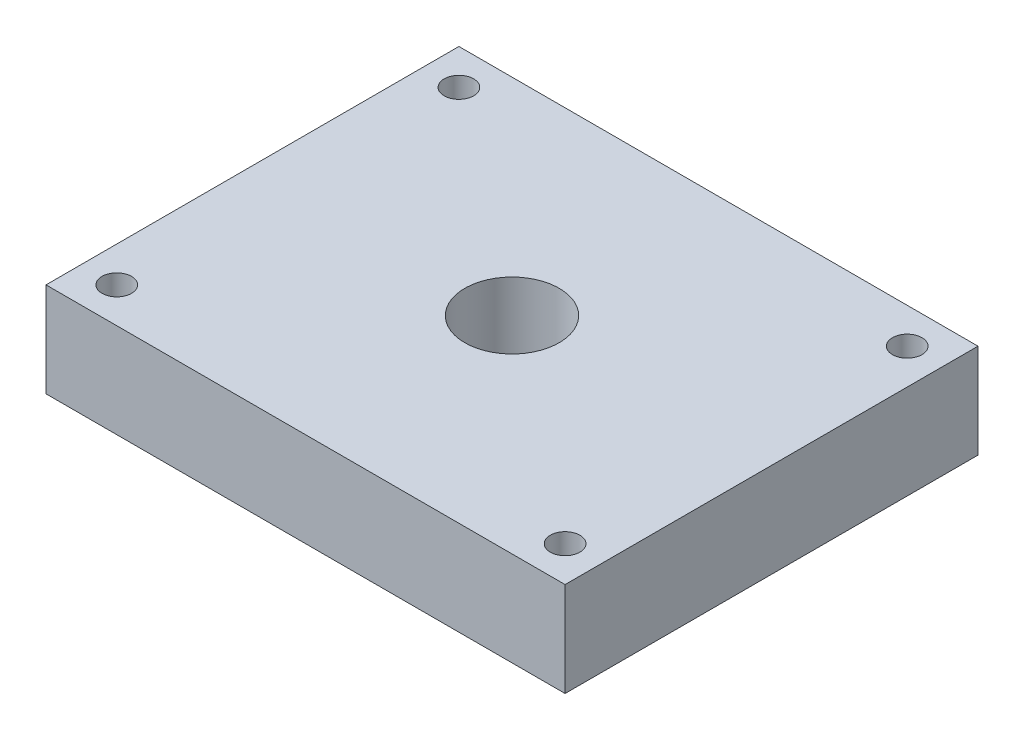
SolidWorks part; units mm, degrees
ref_plane "Front Plane" through (0, 0, 0) normal (0, 0, 1) x (1, 0, 0)
ref_plane "Top Plane" through (0, 0, 0) normal (0, 1, 0) x (1, 0, 0)
ref_plane "Right Plane" through (0, 0, 0) normal (1, 0, 0) x (0, 0, -1)
sketch "Sketch16" plane through (0, 0, 0) normal (0, 1, 0) x (-1, 0, 0)
  line L0 (0, 0) -> (22, 17.5) construction
  line L1 (-22, 17.5) -> (22, 17.5)
  line L2 (-22, 17.5) -> (-22, -17.5)
  line L3 (-22, -17.5) -> (22, -17.5)
  line L4 (22, 17.5) -> (22, -17.5)
  line L5 (-22, 17.5) -> (22, -17.5) construction
  circle A3 centre (-19, 14.5) radius 1.25
  circle A6 centre (19, 14.5) radius 1.25
  circle A7 centre (19, -14.5) radius 1.25
  circle A8 centre (-19, -14.5) radius 1.25
  point P0 (0, 0)
  dimension "D3" = 2
  dimension "D5" = 2.5
  dimension "D8" = 3
  dimension "D1" = 35
  dimension "D2" = 44
  dimension "D4" = 2
  dimension "D9" = 3
extrude "Boss-Extrude1" add sketch "Sketch16" along normal blind 8
sketch "Sketch1" plane through (0, 0, 0) normal (0, 1, 0) x (1, 0, 0)
  circle A2 centre (0, 0) radius 4
  dimension "D1" = 8
extrude "Cut-Extrude3" cut sketch "Sketch1" along normal through all
